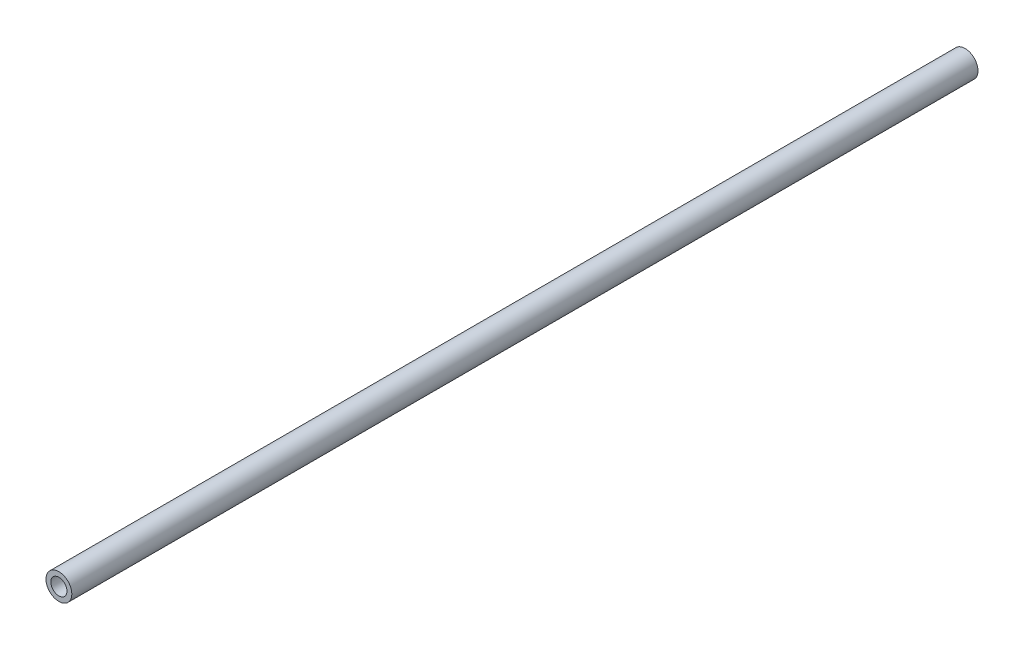
SolidWorks part; units mm, degrees
material "AISI 304"
ref_plane "Front Plane" through (0, 0, 0) normal (0, 0, 1) x (1, 0, 0)
ref_plane "Top Plane" through (0, 0, 0) normal (0, 1, 0) x (1, 0, 0)
ref_plane "Right Plane" through (0, 0, 0) normal (1, 0, 0) x (0, 0, -1)
sketch "Sketch1" plane through (0, 0, 0) normal (0, 0, 1) x (1, 0, 0)
  circle A0 centre (0, 0) radius 8.55
  circle A1 centre (0, 0) radius 5.35
  dimension "D1" = 10.7
  dimension "D2" = 17.1
extrude "Boss-Extrude1" add sketch "Sketch1" against normal blind 600
